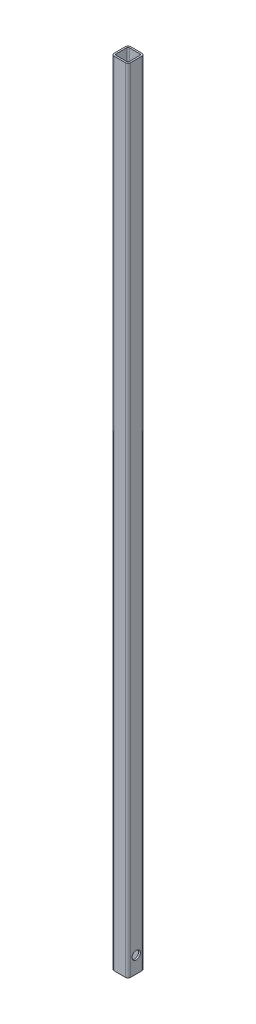
SolidWorks part; units mm, degrees
ref_plane "Front Plane" through (0, 0, 0) normal (0, 0, 1) x (1, 0, 0)
ref_plane "Top Plane" through (0, 0, 0) normal (0, 1, 0) x (1, 0, 0)
ref_plane "Right Plane" through (0, 0, 0) normal (1, 0, 0) x (0, 0, -1)
sketch "Sketch1" plane through (0, 0, 0) normal (0, 1, 0) x (1, 0, 0)
  line L1 (4, 0) -> (21.4, 0)
  line L2 (0, 4) -> (0, 21.4)
  line L3 (4, 25.4) -> (21.4, 25.4)
  line L4 (25.4, 4) -> (25.4, 21.4)
  line L6 (20.86, 2.54) -> (4.54, 2.54)
  line L7 (22.86, 4.54) -> (22.86, 20.86)
  line L8 (2.54, 4.54) -> (2.54, 20.86)
  line L9 (20.86, 22.86) -> (4.54, 22.86)
  line L10 (22.86, 2.54) -> (2.54, 22.86) construction
  line L11 (2.54, 2.54) -> (22.86, 22.86) construction
  arc A0 (2.54, 20.86) -> (4.54, 22.86) centre (4.54, 20.86) cw
  arc A1 (22.86, 20.86) -> (20.86, 22.86) centre (20.86, 20.86) ccw
  arc A2 (22.86, 4.54) -> (20.86, 2.54) centre (20.86, 4.54) cw
  arc A3 (4.54, 2.54) -> (2.54, 4.54) centre (4.54, 4.54) cw
  arc A4 (0, 21.4) -> (4, 25.4) centre (4, 21.4) cw
  arc A5 (21.4, 25.4) -> (25.4, 21.4) centre (21.4, 21.4) cw
  arc A6 (21.4, 0) -> (25.4, 4) centre (21.4, 4) ccw
  arc A7 (4, 0) -> (0, 4) centre (4, 4) cw
  point P9 (12.7, 12.7)
  point P31 (0, 0)
  dimension "D1" = 2
  dimension "D2" = 2
  dimension "D3" = 4
  dimension "D4" = 4
  dimension "D5" = 4
  dimension "D6" = 4
extrude "Boss-Extrude1" add sketch "Sketch1" along normal blind 1219.2
sketch "Sketch3" plane through (25.4, 0, 0) normal (1, 0, 0) x (0, 0, -1)
  circle A0 centre (12.7, 25.4) radius 6.35
extrude "Cut-Extrude2" cut sketch "Sketch3" against normal through all
